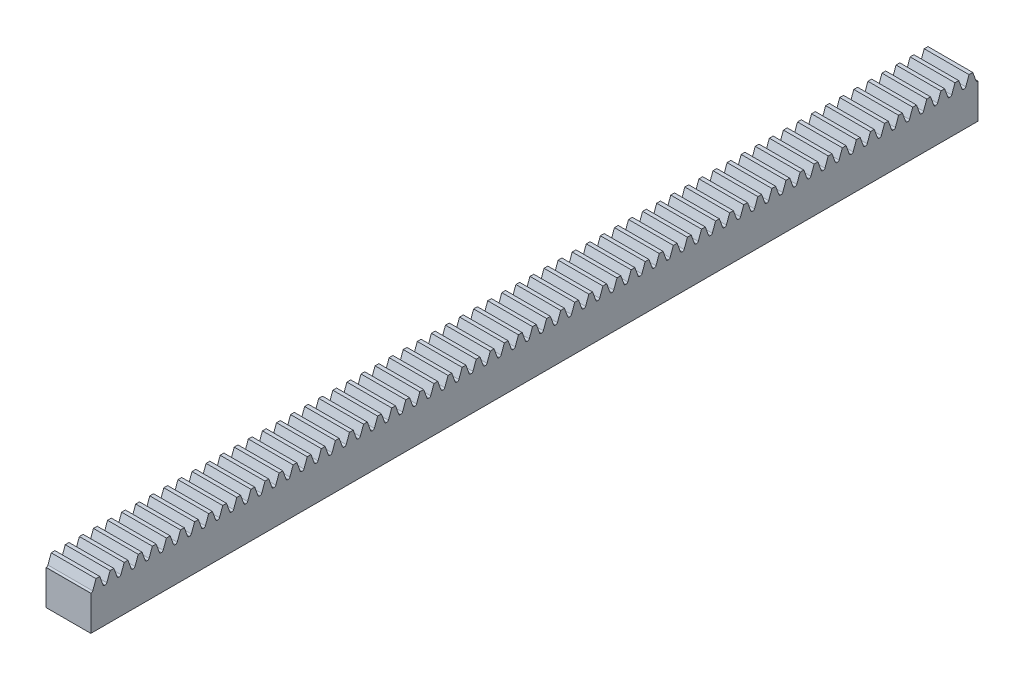
SolidWorks part; units mm, degrees
material "201 Annealed Stainless Steel (SS)"
ref_plane "Front Plane" through (0, 0, 0) normal (0, 0, 1) x (1, 0, 0)
ref_plane "Top Plane" through (0, 0, 0) normal (0, 1, 0) x (1, 0, 0)
ref_plane "Right Plane" through (0, 0, 0) normal (1, 0, 0) x (0, 0, -1)
ref_plane "Plane1" through (7.5, 0, 0) normal (1, 0, 0) x (0, 0, -1)
sketch "Sketch1" plane through (7.5, 0, 0) normal (1, 0, 0) x (0, 0, -1)
  line L0 (0, 15) -> (-296.88, 15)
  line L1 (-296.88, 15) -> (-296.88, 0)
  line L2 (-296.88, 0) -> (0, 0)
  line L3 (0, 0) -> (0, 15)
extrude "Boss-Extrude1" add sketch "Sketch1" against normal blind 15
sketch "Sketch2" plane through (-7.5, 0, 0) normal (-1, 0, 0) x (0, 0, 1)
  line L0 (161.944, 15) -> (158.496, 15)
  line L1 (158.496, 15) -> (159.7244, 11.625)
  line L2 (159.7244, 11.625) -> (160.7156, 11.625)
  line L3 (160.7156, 11.625) -> (161.944, 15)
extrude "Cut-Extrude1" cut sketch "Sketch2" against normal through all
sketch "Sketch3" plane through (-7.5, 0, 0) normal (-1, 0, 0) x (0, 0, 1)
  line L0 (166.656, 15) -> (163.208, 15)
  line L1 (163.208, 15) -> (164.4364, 11.625)
  line L2 (164.4364, 11.625) -> (165.4276, 11.625)
  line L3 (165.4276, 11.625) -> (166.656, 15)
extrude "Cut-Extrude2" cut sketch "Sketch3" against normal through all
sketch "Sketch4" plane through (-7.5, 0, 0) normal (-1, 0, 0) x (0, 0, 1)
  line L0 (171.368, 15) -> (167.92, 15)
  line L1 (167.92, 15) -> (169.1484, 11.625)
  line L2 (169.1484, 11.625) -> (170.1396, 11.625)
  line L3 (170.1396, 11.625) -> (171.368, 15)
extrude "Cut-Extrude3" cut sketch "Sketch4" against normal through all
sketch "Sketch5" plane through (-7.5, 0, 0) normal (-1, 0, 0) x (0, 0, 1)
  line L0 (176.08, 15) -> (172.632, 15)
  line L1 (172.632, 15) -> (173.8604, 11.625)
  line L2 (173.8604, 11.625) -> (174.8516, 11.625)
  line L3 (174.8516, 11.625) -> (176.08, 15)
extrude "Cut-Extrude4" cut sketch "Sketch5" against normal through all
sketch "Sketch6" plane through (-7.5, 0, 0) normal (-1, 0, 0) x (0, 0, 1)
  line L0 (180.792, 15) -> (177.344, 15)
  line L1 (177.344, 15) -> (178.5724, 11.625)
  line L2 (178.5724, 11.625) -> (179.5636, 11.625)
  line L3 (179.5636, 11.625) -> (180.792, 15)
extrude "Cut-Extrude5" cut sketch "Sketch6" against normal through all
sketch "Sketch7" plane through (-7.5, 0, 0) normal (-1, 0, 0) x (0, 0, 1)
  line L0 (185.504, 15) -> (182.056, 15)
  line L1 (182.056, 15) -> (183.2844, 11.625)
  line L2 (183.2844, 11.625) -> (184.2756, 11.625)
  line L3 (184.2756, 11.625) -> (185.504, 15)
extrude "Cut-Extrude6" cut sketch "Sketch7" against normal through all
sketch "Sketch8" plane through (-7.5, 0, 0) normal (-1, 0, 0) x (0, 0, 1)
  line L0 (190.216, 15) -> (186.768, 15)
  line L1 (186.768, 15) -> (187.9964, 11.625)
  line L2 (187.9964, 11.625) -> (188.9876, 11.625)
  line L3 (188.9876, 11.625) -> (190.216, 15)
extrude "Cut-Extrude7" cut sketch "Sketch8" against normal through all
sketch "Sketch9" plane through (-7.5, 0, 0) normal (-1, 0, 0) x (0, 0, 1)
  line L0 (194.928, 15) -> (191.48, 15)
  line L1 (191.48, 15) -> (192.7084, 11.625)
  line L2 (192.7084, 11.625) -> (193.6996, 11.625)
  line L3 (193.6996, 11.625) -> (194.928, 15)
extrude "Cut-Extrude8" cut sketch "Sketch9" against normal through all
sketch "Sketch10" plane through (-7.5, 0, 0) normal (-1, 0, 0) x (0, 0, 1)
  line L0 (199.64, 15) -> (196.192, 15)
  line L1 (196.192, 15) -> (197.4204, 11.625)
  line L2 (197.4204, 11.625) -> (198.4116, 11.625)
  line L3 (198.4116, 11.625) -> (199.64, 15)
extrude "Cut-Extrude9" cut sketch "Sketch10" against normal through all
sketch "Sketch11" plane through (-7.5, 0, 0) normal (-1, 0, 0) x (0, 0, 1)
  line L0 (204.352, 15) -> (200.904, 15)
  line L1 (200.904, 15) -> (202.1324, 11.625)
  line L2 (202.1324, 11.625) -> (203.1236, 11.625)
  line L3 (203.1236, 11.625) -> (204.352, 15)
extrude "Cut-Extrude10" cut sketch "Sketch11" against normal through all
sketch "Sketch12" plane through (-7.5, 0, 0) normal (-1, 0, 0) x (0, 0, 1)
  line L0 (209.064, 15) -> (205.616, 15)
  line L1 (205.616, 15) -> (206.8444, 11.625)
  line L2 (206.8444, 11.625) -> (207.8356, 11.625)
  line L3 (207.8356, 11.625) -> (209.064, 15)
extrude "Cut-Extrude11" cut sketch "Sketch12" against normal through all
sketch "Sketch13" plane through (-7.5, 0, 0) normal (-1, 0, 0) x (0, 0, 1)
  line L0 (213.776, 15) -> (210.328, 15)
  line L1 (210.328, 15) -> (211.5564, 11.625)
  line L2 (211.5564, 11.625) -> (212.5476, 11.625)
  line L3 (212.5476, 11.625) -> (213.776, 15)
extrude "Cut-Extrude12" cut sketch "Sketch13" against normal through all
sketch "Sketch14" plane through (-7.5, 0, 0) normal (-1, 0, 0) x (0, 0, 1)
  line L0 (218.488, 15) -> (215.04, 15)
  line L1 (215.04, 15) -> (216.2684, 11.625)
  line L2 (216.2684, 11.625) -> (217.2596, 11.625)
  line L3 (217.2596, 11.625) -> (218.488, 15)
extrude "Cut-Extrude13" cut sketch "Sketch14" against normal through all
sketch "Sketch15" plane through (-7.5, 0, 0) normal (-1, 0, 0) x (0, 0, 1)
  line L0 (223.2, 15) -> (219.752, 15)
  line L1 (219.752, 15) -> (220.9804, 11.625)
  line L2 (220.9804, 11.625) -> (221.9716, 11.625)
  line L3 (221.9716, 11.625) -> (223.2, 15)
extrude "Cut-Extrude14" cut sketch "Sketch15" against normal through all
sketch "Sketch16" plane through (-7.5, 0, 0) normal (-1, 0, 0) x (0, 0, 1)
  line L0 (227.912, 15) -> (224.464, 15)
  line L1 (224.464, 15) -> (225.6924, 11.625)
  line L2 (225.6924, 11.625) -> (226.6836, 11.625)
  line L3 (226.6836, 11.625) -> (227.912, 15)
extrude "Cut-Extrude15" cut sketch "Sketch16" against normal through all
sketch "Sketch17" plane through (-7.5, 0, 0) normal (-1, 0, 0) x (0, 0, 1)
  line L0 (232.624, 15) -> (229.176, 15)
  line L1 (229.176, 15) -> (230.4044, 11.625)
  line L2 (230.4044, 11.625) -> (231.3956, 11.625)
  line L3 (231.3956, 11.625) -> (232.624, 15)
extrude "Cut-Extrude16" cut sketch "Sketch17" against normal through all
sketch "Sketch18" plane through (-7.5, 0, 0) normal (-1, 0, 0) x (0, 0, 1)
  line L0 (237.336, 15) -> (233.888, 15)
  line L1 (233.888, 15) -> (235.1164, 11.625)
  line L2 (235.1164, 11.625) -> (236.1076, 11.625)
  line L3 (236.1076, 11.625) -> (237.336, 15)
extrude "Cut-Extrude17" cut sketch "Sketch18" against normal through all
sketch "Sketch19" plane through (-7.5, 0, 0) normal (-1, 0, 0) x (0, 0, 1)
  line L0 (242.048, 15) -> (238.6, 15)
  line L1 (238.6, 15) -> (239.8284, 11.625)
  line L2 (239.8284, 11.625) -> (240.8196, 11.625)
  line L3 (240.8196, 11.625) -> (242.048, 15)
extrude "Cut-Extrude18" cut sketch "Sketch19" against normal through all
sketch "Sketch20" plane through (-7.5, 0, 0) normal (-1, 0, 0) x (0, 0, 1)
  line L0 (246.76, 15) -> (243.312, 15)
  line L1 (243.312, 15) -> (244.5404, 11.625)
  line L2 (244.5404, 11.625) -> (245.5316, 11.625)
  line L3 (245.5316, 11.625) -> (246.76, 15)
extrude "Cut-Extrude19" cut sketch "Sketch20" against normal through all
sketch "Sketch21" plane through (-7.5, 0, 0) normal (-1, 0, 0) x (0, 0, 1)
  line L0 (251.472, 15) -> (248.024, 15)
  line L1 (248.024, 15) -> (249.2524, 11.625)
  line L2 (249.2524, 11.625) -> (250.2436, 11.625)
  line L3 (250.2436, 11.625) -> (251.472, 15)
extrude "Cut-Extrude20" cut sketch "Sketch21" against normal through all
sketch "Sketch22" plane through (-7.5, 0, 0) normal (-1, 0, 0) x (0, 0, 1)
  line L0 (256.184, 15) -> (252.736, 15)
  line L1 (252.736, 15) -> (253.9644, 11.625)
  line L2 (253.9644, 11.625) -> (254.9556, 11.625)
  line L3 (254.9556, 11.625) -> (256.184, 15)
extrude "Cut-Extrude21" cut sketch "Sketch22" against normal through all
sketch "Sketch23" plane through (-7.5, 0, 0) normal (-1, 0, 0) x (0, 0, 1)
  line L0 (260.896, 15) -> (257.448, 15)
  line L1 (257.448, 15) -> (258.6764, 11.625)
  line L2 (258.6764, 11.625) -> (259.6676, 11.625)
  line L3 (259.6676, 11.625) -> (260.896, 15)
extrude "Cut-Extrude22" cut sketch "Sketch23" against normal through all
sketch "Sketch24" plane through (-7.5, 0, 0) normal (-1, 0, 0) x (0, 0, 1)
  line L0 (265.608, 15) -> (262.16, 15)
  line L1 (262.16, 15) -> (263.3884, 11.625)
  line L2 (263.3884, 11.625) -> (264.3796, 11.625)
  line L3 (264.3796, 11.625) -> (265.608, 15)
extrude "Cut-Extrude23" cut sketch "Sketch24" against normal through all
sketch "Sketch25" plane through (-7.5, 0, 0) normal (-1, 0, 0) x (0, 0, 1)
  line L0 (270.32, 15) -> (266.872, 15)
  line L1 (266.872, 15) -> (268.1004, 11.625)
  line L2 (268.1004, 11.625) -> (269.0916, 11.625)
  line L3 (269.0916, 11.625) -> (270.32, 15)
extrude "Cut-Extrude24" cut sketch "Sketch25" against normal through all
sketch "Sketch26" plane through (-7.5, 0, 0) normal (-1, 0, 0) x (0, 0, 1)
  line L0 (275.032, 15) -> (271.584, 15)
  line L1 (271.584, 15) -> (272.8124, 11.625)
  line L2 (272.8124, 11.625) -> (273.8036, 11.625)
  line L3 (273.8036, 11.625) -> (275.032, 15)
extrude "Cut-Extrude25" cut sketch "Sketch26" against normal through all
sketch "Sketch27" plane through (-7.5, 0, 0) normal (-1, 0, 0) x (0, 0, 1)
  line L0 (279.744, 15) -> (276.296, 15)
  line L1 (276.296, 15) -> (277.5244, 11.625)
  line L2 (277.5244, 11.625) -> (278.5156, 11.625)
  line L3 (278.5156, 11.625) -> (279.744, 15)
extrude "Cut-Extrude26" cut sketch "Sketch27" against normal through all
sketch "Sketch28" plane through (-7.5, 0, 0) normal (-1, 0, 0) x (0, 0, 1)
  line L0 (284.456, 15) -> (281.008, 15)
  line L1 (281.008, 15) -> (282.2364, 11.625)
  line L2 (282.2364, 11.625) -> (283.2276, 11.625)
  line L3 (283.2276, 11.625) -> (284.456, 15)
extrude "Cut-Extrude27" cut sketch "Sketch28" against normal through all
sketch "Sketch29" plane through (-7.5, 0, 0) normal (-1, 0, 0) x (0, 0, 1)
  line L0 (289.168, 15) -> (285.72, 15)
  line L1 (285.72, 15) -> (286.9484, 11.625)
  line L2 (286.9484, 11.625) -> (287.9396, 11.625)
  line L3 (287.9396, 11.625) -> (289.168, 15)
extrude "Cut-Extrude28" cut sketch "Sketch29" against normal through all
sketch "Sketch30" plane through (-7.5, 0, 0) normal (-1, 0, 0) x (0, 0, 1)
  line L0 (293.88, 15) -> (290.432, 15)
  line L1 (290.432, 15) -> (291.6604, 11.625)
  line L2 (291.6604, 11.625) -> (292.6516, 11.625)
  line L3 (292.6516, 11.625) -> (293.88, 15)
extrude "Cut-Extrude29" cut sketch "Sketch30" against normal through all
sketch "Sketch31" plane through (-7.5, 0, 0) normal (-1, 0, 0) x (0, 0, 1)
  line L0 (296.88, 15) -> (295.144, 15)
  line L1 (295.144, 15) -> (296.3724, 11.625)
  line L2 (296.3724, 11.625) -> (296.88, 11.625)
  line L3 (296.88, 11.625) -> (296.88, 15)
extrude "Cut-Extrude30" cut sketch "Sketch31" against normal through all
sketch "Sketch32" plane through (-7.5, 0, 0) normal (-1, 0, 0) x (0, 0, 1)
  line L0 (0, 15) -> (0, 11.625)
  line L1 (0, 11.625) -> (0.5076, 11.625)
  line L2 (0.5076, 11.625) -> (1.736, 15)
  line L3 (1.736, 15) -> (0, 15)
extrude "Cut-Extrude31" cut sketch "Sketch32" against normal through all
sketch "Sketch33" plane through (-7.5, 0, 0) normal (-1, 0, 0) x (0, 0, 1)
  line L0 (6.448, 15) -> (3, 15)
  line L1 (3, 15) -> (4.2284, 11.625)
  line L2 (4.2284, 11.625) -> (5.2196, 11.625)
  line L3 (5.2196, 11.625) -> (6.448, 15)
extrude "Cut-Extrude32" cut sketch "Sketch33" against normal through all
sketch "Sketch34" plane through (-7.5, 0, 0) normal (-1, 0, 0) x (0, 0, 1)
  line L0 (11.16, 15) -> (7.712, 15)
  line L1 (7.712, 15) -> (8.9404, 11.625)
  line L2 (8.9404, 11.625) -> (9.9316, 11.625)
  line L3 (9.9316, 11.625) -> (11.16, 15)
extrude "Cut-Extrude33" cut sketch "Sketch34" against normal through all
sketch "Sketch35" plane through (-7.5, 0, 0) normal (-1, 0, 0) x (0, 0, 1)
  line L0 (15.872, 15) -> (12.424, 15)
  line L1 (12.424, 15) -> (13.6524, 11.625)
  line L2 (13.6524, 11.625) -> (14.6436, 11.625)
  line L3 (14.6436, 11.625) -> (15.872, 15)
extrude "Cut-Extrude34" cut sketch "Sketch35" against normal through all
sketch "Sketch36" plane through (-7.5, 0, 0) normal (-1, 0, 0) x (0, 0, 1)
  line L0 (20.584, 15) -> (17.136, 15)
  line L1 (17.136, 15) -> (18.3644, 11.625)
  line L2 (18.3644, 11.625) -> (19.3556, 11.625)
  line L3 (19.3556, 11.625) -> (20.584, 15)
extrude "Cut-Extrude35" cut sketch "Sketch36" against normal through all
sketch "Sketch37" plane through (-7.5, 0, 0) normal (-1, 0, 0) x (0, 0, 1)
  line L0 (25.296, 15) -> (21.848, 15)
  line L1 (21.848, 15) -> (23.0764, 11.625)
  line L2 (23.0764, 11.625) -> (24.0676, 11.625)
  line L3 (24.0676, 11.625) -> (25.296, 15)
extrude "Cut-Extrude36" cut sketch "Sketch37" against normal through all
sketch "Sketch38" plane through (-7.5, 0, 0) normal (-1, 0, 0) x (0, 0, 1)
  line L0 (30.008, 15) -> (26.56, 15)
  line L1 (26.56, 15) -> (27.7884, 11.625)
  line L2 (27.7884, 11.625) -> (28.7796, 11.625)
  line L3 (28.7796, 11.625) -> (30.008, 15)
extrude "Cut-Extrude37" cut sketch "Sketch38" against normal through all
sketch "Sketch39" plane through (-7.5, 0, 0) normal (-1, 0, 0) x (0, 0, 1)
  line L0 (34.72, 15) -> (31.272, 15)
  line L1 (31.272, 15) -> (32.5004, 11.625)
  line L2 (32.5004, 11.625) -> (33.4916, 11.625)
  line L3 (33.4916, 11.625) -> (34.72, 15)
extrude "Cut-Extrude38" cut sketch "Sketch39" against normal through all
sketch "Sketch40" plane through (-7.5, 0, 0) normal (-1, 0, 0) x (0, 0, 1)
  line L0 (39.432, 15) -> (35.984, 15)
  line L1 (35.984, 15) -> (37.2124, 11.625)
  line L2 (37.2124, 11.625) -> (38.2036, 11.625)
  line L3 (38.2036, 11.625) -> (39.432, 15)
extrude "Cut-Extrude39" cut sketch "Sketch40" against normal through all
sketch "Sketch41" plane through (-7.5, 0, 0) normal (-1, 0, 0) x (0, 0, 1)
  line L0 (44.144, 15) -> (40.696, 15)
  line L1 (40.696, 15) -> (41.9244, 11.625)
  line L2 (41.9244, 11.625) -> (42.9156, 11.625)
  line L3 (42.9156, 11.625) -> (44.144, 15)
extrude "Cut-Extrude40" cut sketch "Sketch41" against normal through all
sketch "Sketch42" plane through (-7.5, 0, 0) normal (-1, 0, 0) x (0, 0, 1)
  line L0 (48.856, 15) -> (45.408, 15)
  line L1 (45.408, 15) -> (46.6364, 11.625)
  line L2 (46.6364, 11.625) -> (47.6276, 11.625)
  line L3 (47.6276, 11.625) -> (48.856, 15)
extrude "Cut-Extrude41" cut sketch "Sketch42" against normal through all
sketch "Sketch43" plane through (-7.5, 0, 0) normal (-1, 0, 0) x (0, 0, 1)
  line L0 (53.568, 15) -> (50.12, 15)
  line L1 (50.12, 15) -> (51.3484, 11.625)
  line L2 (51.3484, 11.625) -> (52.3396, 11.625)
  line L3 (52.3396, 11.625) -> (53.568, 15)
extrude "Cut-Extrude42" cut sketch "Sketch43" against normal through all
sketch "Sketch44" plane through (-7.5, 0, 0) normal (-1, 0, 0) x (0, 0, 1)
  line L0 (58.28, 15) -> (54.832, 15)
  line L1 (54.832, 15) -> (56.0604, 11.625)
  line L2 (56.0604, 11.625) -> (57.0516, 11.625)
  line L3 (57.0516, 11.625) -> (58.28, 15)
extrude "Cut-Extrude43" cut sketch "Sketch44" against normal through all
sketch "Sketch45" plane through (-7.5, 0, 0) normal (-1, 0, 0) x (0, 0, 1)
  line L0 (62.992, 15) -> (59.544, 15)
  line L1 (59.544, 15) -> (60.7724, 11.625)
  line L2 (60.7724, 11.625) -> (61.7636, 11.625)
  line L3 (61.7636, 11.625) -> (62.992, 15)
extrude "Cut-Extrude44" cut sketch "Sketch45" against normal through all
sketch "Sketch46" plane through (-7.5, 0, 0) normal (-1, 0, 0) x (0, 0, 1)
  line L0 (67.704, 15) -> (64.256, 15)
  line L1 (64.256, 15) -> (65.4844, 11.625)
  line L2 (65.4844, 11.625) -> (66.4756, 11.625)
  line L3 (66.4756, 11.625) -> (67.704, 15)
extrude "Cut-Extrude45" cut sketch "Sketch46" against normal through all
sketch "Sketch47" plane through (-7.5, 0, 0) normal (-1, 0, 0) x (0, 0, 1)
  line L0 (72.416, 15) -> (68.968, 15)
  line L1 (68.968, 15) -> (70.1964, 11.625)
  line L2 (70.1964, 11.625) -> (71.1876, 11.625)
  line L3 (71.1876, 11.625) -> (72.416, 15)
extrude "Cut-Extrude46" cut sketch "Sketch47" against normal through all
sketch "Sketch48" plane through (-7.5, 0, 0) normal (-1, 0, 0) x (0, 0, 1)
  line L0 (77.128, 15) -> (73.68, 15)
  line L1 (73.68, 15) -> (74.9084, 11.625)
  line L2 (74.9084, 11.625) -> (75.8996, 11.625)
  line L3 (75.8996, 11.625) -> (77.128, 15)
extrude "Cut-Extrude47" cut sketch "Sketch48" against normal through all
sketch "Sketch49" plane through (-7.5, 0, 0) normal (-1, 0, 0) x (0, 0, 1)
  line L0 (81.84, 15) -> (78.392, 15)
  line L1 (78.392, 15) -> (79.6204, 11.625)
  line L2 (79.6204, 11.625) -> (80.6116, 11.625)
  line L3 (80.6116, 11.625) -> (81.84, 15)
extrude "Cut-Extrude48" cut sketch "Sketch49" against normal through all
sketch "Sketch50" plane through (-7.5, 0, 0) normal (-1, 0, 0) x (0, 0, 1)
  line L0 (86.552, 15) -> (83.104, 15)
  line L1 (83.104, 15) -> (84.3324, 11.625)
  line L2 (84.3324, 11.625) -> (85.3236, 11.625)
  line L3 (85.3236, 11.625) -> (86.552, 15)
extrude "Cut-Extrude49" cut sketch "Sketch50" against normal through all
sketch "Sketch51" plane through (-7.5, 0, 0) normal (-1, 0, 0) x (0, 0, 1)
  line L0 (91.264, 15) -> (87.816, 15)
  line L1 (87.816, 15) -> (89.0444, 11.625)
  line L2 (89.0444, 11.625) -> (90.0356, 11.625)
  line L3 (90.0356, 11.625) -> (91.264, 15)
extrude "Cut-Extrude50" cut sketch "Sketch51" against normal through all
sketch "Sketch52" plane through (-7.5, 0, 0) normal (-1, 0, 0) x (0, 0, 1)
  line L0 (95.976, 15) -> (92.528, 15)
  line L1 (92.528, 15) -> (93.7564, 11.625)
  line L2 (93.7564, 11.625) -> (94.7476, 11.625)
  line L3 (94.7476, 11.625) -> (95.976, 15)
extrude "Cut-Extrude51" cut sketch "Sketch52" against normal through all
sketch "Sketch53" plane through (-7.5, 0, 0) normal (-1, 0, 0) x (0, 0, 1)
  line L0 (100.688, 15) -> (97.24, 15)
  line L1 (97.24, 15) -> (98.4684, 11.625)
  line L2 (98.4684, 11.625) -> (99.4596, 11.625)
  line L3 (99.4596, 11.625) -> (100.688, 15)
extrude "Cut-Extrude52" cut sketch "Sketch53" against normal through all
sketch "Sketch54" plane through (-7.5, 0, 0) normal (-1, 0, 0) x (0, 0, 1)
  line L0 (105.4, 15) -> (101.952, 15)
  line L1 (101.952, 15) -> (103.1804, 11.625)
  line L2 (103.1804, 11.625) -> (104.1716, 11.625)
  line L3 (104.1716, 11.625) -> (105.4, 15)
extrude "Cut-Extrude53" cut sketch "Sketch54" against normal through all
sketch "Sketch55" plane through (-7.5, 0, 0) normal (-1, 0, 0) x (0, 0, 1)
  line L0 (110.112, 15) -> (106.664, 15)
  line L1 (106.664, 15) -> (107.8924, 11.625)
  line L2 (107.8924, 11.625) -> (108.8836, 11.625)
  line L3 (108.8836, 11.625) -> (110.112, 15)
extrude "Cut-Extrude54" cut sketch "Sketch55" against normal through all
sketch "Sketch56" plane through (-7.5, 0, 0) normal (-1, 0, 0) x (0, 0, 1)
  line L0 (114.824, 15) -> (111.376, 15)
  line L1 (111.376, 15) -> (112.6044, 11.625)
  line L2 (112.6044, 11.625) -> (113.5956, 11.625)
  line L3 (113.5956, 11.625) -> (114.824, 15)
extrude "Cut-Extrude55" cut sketch "Sketch56" against normal through all
sketch "Sketch57" plane through (-7.5, 0, 0) normal (-1, 0, 0) x (0, 0, 1)
  line L0 (119.536, 15) -> (116.088, 15)
  line L1 (116.088, 15) -> (117.3164, 11.625)
  line L2 (117.3164, 11.625) -> (118.3076, 11.625)
  line L3 (118.3076, 11.625) -> (119.536, 15)
extrude "Cut-Extrude56" cut sketch "Sketch57" against normal through all
sketch "Sketch58" plane through (-7.5, 0, 0) normal (-1, 0, 0) x (0, 0, 1)
  line L0 (124.248, 15) -> (120.8, 15)
  line L1 (120.8, 15) -> (122.0284, 11.625)
  line L2 (122.0284, 11.625) -> (123.0196, 11.625)
  line L3 (123.0196, 11.625) -> (124.248, 15)
extrude "Cut-Extrude57" cut sketch "Sketch58" against normal through all
sketch "Sketch59" plane through (-7.5, 0, 0) normal (-1, 0, 0) x (0, 0, 1)
  line L0 (128.96, 15) -> (125.512, 15)
  line L1 (125.512, 15) -> (126.7404, 11.625)
  line L2 (126.7404, 11.625) -> (127.7316, 11.625)
  line L3 (127.7316, 11.625) -> (128.96, 15)
extrude "Cut-Extrude58" cut sketch "Sketch59" against normal through all
sketch "Sketch60" plane through (-7.5, 0, 0) normal (-1, 0, 0) x (0, 0, 1)
  line L0 (133.672, 15) -> (130.224, 15)
  line L1 (130.224, 15) -> (131.4524, 11.625)
  line L2 (131.4524, 11.625) -> (132.4436, 11.625)
  line L3 (132.4436, 11.625) -> (133.672, 15)
extrude "Cut-Extrude59" cut sketch "Sketch60" against normal through all
sketch "Sketch61" plane through (-7.5, 0, 0) normal (-1, 0, 0) x (0, 0, 1)
  line L0 (138.384, 15) -> (134.936, 15)
  line L1 (134.936, 15) -> (136.1644, 11.625)
  line L2 (136.1644, 11.625) -> (137.1556, 11.625)
  line L3 (137.1556, 11.625) -> (138.384, 15)
extrude "Cut-Extrude60" cut sketch "Sketch61" against normal through all
sketch "Sketch62" plane through (-7.5, 0, 0) normal (-1, 0, 0) x (0, 0, 1)
  line L0 (143.096, 15) -> (139.648, 15)
  line L1 (139.648, 15) -> (140.8764, 11.625)
  line L2 (140.8764, 11.625) -> (141.8676, 11.625)
  line L3 (141.8676, 11.625) -> (143.096, 15)
extrude "Cut-Extrude61" cut sketch "Sketch62" against normal through all
sketch "Sketch63" plane through (-7.5, 0, 0) normal (-1, 0, 0) x (0, 0, 1)
  line L0 (147.808, 15) -> (144.36, 15)
  line L1 (144.36, 15) -> (145.5884, 11.625)
  line L2 (145.5884, 11.625) -> (146.5796, 11.625)
  line L3 (146.5796, 11.625) -> (147.808, 15)
extrude "Cut-Extrude62" cut sketch "Sketch63" against normal through all
sketch "Sketch64" plane through (-7.5, 0, 0) normal (-1, 0, 0) x (0, 0, 1)
  line L0 (152.52, 15) -> (149.072, 15)
  line L1 (149.072, 15) -> (150.3004, 11.625)
  line L2 (150.3004, 11.625) -> (151.2916, 11.625)
  line L3 (151.2916, 11.625) -> (152.52, 15)
extrude "Cut-Extrude63" cut sketch "Sketch64" against normal through all
sketch "Sketch65" plane through (-7.5, 0, 0) normal (-1, 0, 0) x (0, 0, 1)
  line L0 (157.232, 15) -> (153.784, 15)
  line L1 (153.784, 15) -> (155.0124, 11.625)
  line L2 (155.0124, 11.625) -> (156.0036, 11.625)
  line L3 (156.0036, 11.625) -> (157.232, 15)
extrude "Cut-Extrude64" cut sketch "Sketch65" against normal through all
hole_wizard "M3 Clearance Hole1" positions "Sketch67" profile "Sketch66" hole size "M3" standard "ANSI Metric"
sketch "Sketch67" plane through (0, 0, 0) normal (0, -1, 0) x (-1, 0, 0)
  point P0 (0, -58.44)
  point P1 (0, -238.44)
sketch "Sketch66" plane through (0, 0, 58.44) normal (1, 0, 0) x (0, 0, -1)
  line L0 (0, 0) -> (0, 8)
  line L1 (0, 8) -> (1.621, 7.0641)
  line L2 (1.621, 7.0641) -> (1.621, 0)
  line L5 (1.621, 0) -> (0, 0)
  line L10 (0, 8) -> (-1.621, 7.0641) construction
  line L11 (0, -6.35) -> (0, 107.95) construction
  dimension "Hole Dia." = 3.242
  dimension "Hole Depth" = 7.0641
  dimension "Drill Angle" = 120
chamfer "Chamfer1" distance 0.379 angle 45 2 edges at (0, 0, 56.819) (0, 0, 236.819)
fillet "Fillet1" radius 0.57 126 edges at (0, 11.625, 8.9404) (0, 11.625, 84.3324) (0, 11.625, 46.6364) (0, 11.625, 155.0124) (0, 11.625, 122.0284) (0, 11.625, 159.7244) (0, 11.625, 27.7884) (0, 11.625, 160.7156) (0, 11.625, 65.4844) (0, 11.625, 164.4364) (0, 11.625, 103.1804) (0, 11.625, 165.4276) (0, 11.625, 140.8764) (0, 11.625, 169.1484) (0, 11.625, 18.3644) (0, 11.625, 170.1396) (0, 11.625, 37.2124) (0, 11.625, 173.8604) (0, 11.625, 56.0604) (0, 11.625, 174.8516) (0, 11.625, 74.9084) (0, 11.625, 178.5724) (0, 11.625, 93.7564) (0, 11.625, 179.5636) (0, 11.625, 112.6044) (0, 11.625, 183.2844) (0, 11.625, 131.4524) (0, 11.625, 184.2756) (0, 11.625, 150.3004) (0, 11.625, 187.9964) (0, 11.625, 13.6524) (0, 11.625, 188.9876) (0, 11.625, 23.0764) (0, 11.625, 192.7084) (0, 11.625, 32.5004) (0, 11.625, 193.6996) (0, 11.625, 41.9244) (0, 11.625, 197.4204) (0, 11.625, 51.3484) (0, 11.625, 198.4116) (0, 11.625, 60.7724) (0, 11.625, 202.1324) (0, 11.625, 70.1964) (0, 11.625, 203.1236) (0, 11.625, 79.6204) (0, 11.625, 206.8444) (0, 11.625, 89.0444) (0, 11.625, 207.8356) (0, 11.625, 98.4684) (0, 11.625, 211.5564) (0, 11.625, 107.8924) (0, 11.625, 212.5476) (0, 11.625, 117.3164) (0, 11.625, 216.2684) (0, 11.625, 126.7404) (0, 11.625, 217.2596) (0, 11.625, 136.1644) (0, 11.625, 220.9804) (0, 11.625, 145.5884) (0, 11.625, 221.9716) (0, 11.625, 156.0036) (0, 11.625, 225.6924) (0, 11.625, 9.9316) (0, 11.625, 226.6836) (0, 11.625, 14.6436) (0, 11.625, 230.4044) (0, 11.625, 19.3556) (0, 11.625, 231.3956) (0, 11.625, 24.0676) (0, 11.625, 235.1164) (0, 11.625, 28.7796) (0, 11.625, 236.1076) (0, 11.625, 33.4916) (0, 11.625, 239.8284) (0, 11.625, 38.2036) (0, 11.625, 240.8196) (0, 11.625, 42.9156) (0, 11.625, 244.5404) (0, 11.625, 47.6276) (0, 11.625, 245.5316) (0, 11.625, 52.3396) (0, 11.625, 249.2524) (0, 11.625, 57.0516) (0, 11.625, 250.2436) (0, 11.625, 61.7636) (0, 11.625, 253.9644) (0, 11.625, 66.4756) (0, 11.625, 254.9556) (0, 11.625, 71.1876) (0, 11.625, 258.6764) (0, 11.625, 75.8996) (0, 11.625, 259.6676) (0, 11.625, 80.6116) (0, 11.625, 263.3884) (0, 11.625, 85.3236) (0, 11.625, 264.3796) (0, 11.625, 90.0356) (0, 11.625, 268.1004) (0, 11.625, 94.7476) (0, 11.625, 269.0916) (0, 11.625, 99.4596) (0, 11.625, 272.8124) (0, 11.625, 104.1716) (0, 11.625, 273.8036) (0, 11.625, 108.8836) (0, 11.625, 277.5244) (0, 11.625, 113.5956) (0, 11.625, 278.5156) (0, 11.625, 118.3076) (0, 11.625, 282.2364) (0, 11.625, 123.0196) (0, 11.625, 283.2276) (0, 11.625, 127.7316) (0, 11.625, 286.9484) (0, 11.625, 132.4436) (0, 11.625, 287.9396) (0, 11.625, 137.1556) (0, 11.625, 291.6604) (0, 11.625, 141.8676) (0, 11.625, 292.6516) (0, 11.625, 146.5796) (0, 11.625, 296.3724) (0, 11.625, 151.2916) (0, 11.625, 0.5076) (0, 11.625, 5.2196) (0, 11.625, 4.2284)
sketch "Sketch68" plane through (7.5, 0, 0) normal (1, 0, 0) x (0, 0, -1)
  line L0 (-296.88, 13.5) -> (0, 13.5) construction
  line L1 (-296.88, 11.625) -> (-296.88, 0) construction
  line L2 (0, 0) -> (0, 11.625) construction
  line L3 (-296.88, 0) -> (0, 0) construction
  point P2 (0, 0)
  point P5 (0, 0)
  dimension "D1" = 13.5
